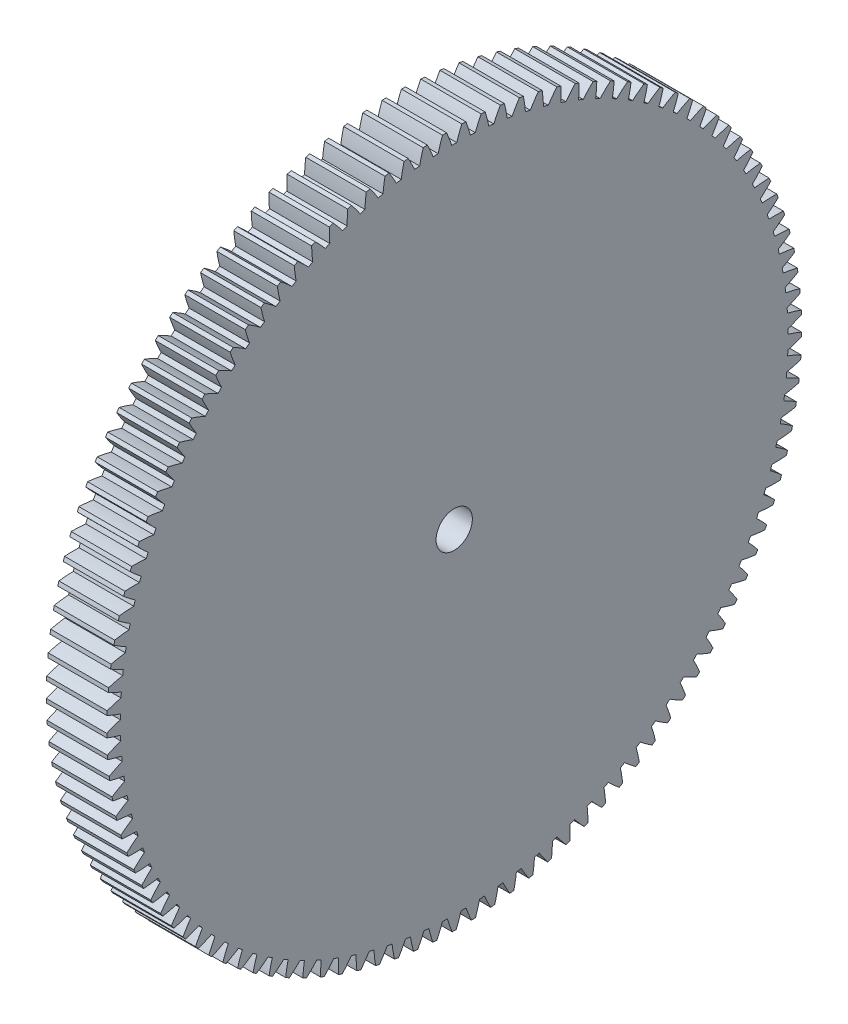
SolidWorks part; units mm, degrees
material "1.0035 (S185)"
ref_plane "Plane1" through (0, 0, 0) normal (0, 0, 1) x (1, 0, 0)
ref_plane "Plane2" through (0, 0, 0) normal (0, 1, 0) x (1, 0, 0)
ref_plane "Plane3" through (0, 0, 0) normal (1, 0, 0) x (0, 0, -1)
sketch "HoldingSke" plane through (0, 0, 0) normal (0, 1, 0) x (1, 0, 0)
  line L0 (0, 0) -> (-0.7815, -1.841)
  line L1 (-15, 0) -> (100, 0) construction
  line L2 (0, 0) -> (-2.1039, 2.3779)
  line L3 (0, 0) -> (-11.863, 4.5341)
  line L4 (0, 0) -> (-3.3744, 7.9495)
  line L5 (0, 0) -> (-46.8476, -17.4728)
  line L6 (0, 0) -> (-4.1448, -2.7965)
  line L7 (-2.1039, 2.3779) -> (8.6586, 51.2059)
  line L8 (-76.2, 54.61) -> (-75.7, 54.61)
  line L9 (-71.009, 38.7566) -> (-53.1078, 45.2721)
  line L10 (-76.2, 71.12) -> (104.1128, 71.12)
  line L11 (0, 0) -> (-5, 0)
  line L12 (-76.2, 101.6) -> (-76.181, 101.6)
  line L13 (24.9733, 27.94) -> (52.9518, 28.4284)
  line L14 (24.9733, 27.94) -> (24.9743, 27.94)
  line L15 (24.9733, 27.94) -> (100.4006, 29.5858)
  line L16 (-63.627, -0.5) -> (-12.827, -0.5)
  circle A0 centre (0, 0) radius 1.5
  circle A1 centre (0, 0) radius 27.624
  circle A2 centre (0, 0) radius 37.5
  circle A3 centre (0, 0) radius 1.5
  dimension "MHD" = 55.248
  dimension "Hub_dia" = 75
  dimension "Bore" = 3
  dimension "MBD" = 3
  dimension "Num_teeth" = 113
  dimension "Pitch_radius" = 180.3128
  dimension "Pitch" = 2
  dimension "Width" = 5
  dimension "Overall_len" = 50
  dimension "Show_teeth" = 113
  dimension "Thickness" = 5
  dimension "OAL" = 50.0001
  dimension "T_dim" = 0.5
  dimension "Ap" = 20
  dimension "H" = 19.05
  dimension "Backlash" = 0.019
  dimension "Addendum_fac" = 1
  dimension "Dedendum_fac" = 1.25
  dimension "Clearance_fac" = 0.25
  dimension "Dedendum_add" = 0.001
  dimension "Module" = 0.5
sketch "BasProSke" plane through (0, 0, 0) normal (0, 1, 0) x (1, 0, 0)
  line L0 (-10, 0) -> (60, 0) construction
  line L1 (0, 0) -> (0, 28.75)
  line L2 (0, 0) -> (5, 0)
  line L3 (5, 0) -> (5, 28.75)
  line L4 (5, 28.75) -> (0, 28.75)
  dimension "Diameter" = 57.5
  dimension "Thickness" = 5
revolve "Base-Revolve" add sketch "BasProSke" angle 360 about L0
sketch "TooCutSke" plane through (0, 0, 0) normal (1, 0, 0) x (0, 0, -1)
  line L1 (0, 0) -> (0, 107) construction
  line L2 (0, 0) -> (-0.4259, 28.2468) construction
  line L3 (0, 0) -> (-1.5705, 56.4736) construction
  line L4 (-0.4259, 28.2468) -> (-0.7852, 28.2368) construction
  arc A0 (0.2058, 27.6232) -> (-0.2058, 27.6232) centre (0, 0) ccw
  arc A1 (0.6425, 28.7682) -> (-0.6425, 28.7682) centre (0, 0) ccw
  circle A2 centre (0, 0) radius 28.25 construction
  circle A3 centre (0, 0) radius 26.5463 construction
  arc A4 (-0.2058, 27.6232) -> (-0.6425, 28.7682) centre (-10.9669, 24.1751) ccw
  arc A5 (0.6425, 28.7682) -> (0.2058, 27.6232) centre (10.9669, 24.1751) ccw
  dimension "Root_dia" = 55.248
  dimension "Overcut_dia" = 57.5508
  dimension "Pitch_dia" = 56.5
  dimension "Base_dia" = 53.0926
  dimension "Flank_rad" = 11.3
  dimension "Half_ang" = 1.593
  dimension "Half_CT" = 0.3594
extrude "ToothCut" cut sketch "TooCutSke" along normal through all
fillet "Breaks" [suppressed] radius 0.01
fillet "RootFillets" [suppressed] radius 0.126
pattern_circular "TeethCuts" count 113 every 3.186 about axis through (-10, 0, 0) along (1, 0, 0) of "ToothCut", "RootFillets", "Breaks"
sketch "HubNeaOneSke" plane through (0, 0, 0) normal (-1, 0, 0) x (0, 0, 1)
  circle A0 centre (0, 0) radius 27.624
  dimension "Diameter" = 55.248
extrude "HubNearOne" [suppressed] add sketch "HubNeaOneSke" along normal blind 45.0001
sketch "HubNeaBotSke" plane through (0, 0, 0) normal (-1, 0, 0) x (0, 0, 1)
  circle A0 centre (0, 0) radius 27.624
  dimension "Diameter" = 55.248
extrude "HubNearBoth" [suppressed] add sketch "HubNeaBotSke" along normal blind 22.5
ref_plane "FarPln" through (5, 0, 0) normal (1, 0, 0) x (0, 0, -1)
sketch "HubFarSke" plane through (5, 0, 0) normal (1, 0, 0) x (0, 0, -1)
  circle A0 centre (0, 0) radius 27.624
  dimension "Diameter" = 55.248
extrude "HubFar" [suppressed] add sketch "HubFarSke" along normal blind 22.5
sketch "BorSke" plane through (0, 0, 0) normal (1, 0, 0) x (0, 0, -1)
  circle A0 centre (0, 0) radius 1.5
  dimension "Diameter" = 3
extrude "Bore" cut sketch "BorSke" along normal mid plane 100.0001
sketch "KeySke" plane through (0, 0, 0) normal (1, 0, 0) x (0, 0, -1)
  line L0 (-0.6, 0) -> (-0.6, 2)
  line L1 (-0.6, 2) -> (0.6, 2)
  line L2 (0.6, 2) -> (0.6, 0)
  line L3 (0, 0) -> (0, 34) construction
  line L4 (-0.6, 0) -> (0.6, 0)
  dimension "Offset" = 2
  dimension "Width" = 1.2
extrude "Keyway" [suppressed] cut sketch "KeySke" along normal mid plane 100.0001
pattern_circular "Keyway2" [suppressed] count 2 every 90 about axis through (-10, 0, 0) along (1, 0, 0)
equation "' \"Module@HoldingSke\" = 6.35"
equation "' \"Num_teeth@HoldingSke\" = 12"
equation "' \"Ap@HoldingSke\" =  20"
equation "' \"Width@HoldingSke\" = 0.5 * 25.4"
equation "' \"Hub_dia@HoldingSke\"= 1 * 25.4"
equation "' \"Overall_len@HoldingSke\" = 1.0 * 25.4"
equation "' \"Bore@HoldingSke\" = 0.75 * 25.4"
equation "' \"T_dim@HoldingSke\" = 0.1 * 25.4"
equation "' \"Width@KeySke\" = 0.25 * 25.4"
equation "' \"Show_teeth@HoldingSke\" = 13"
equation "' \"Backlash@HoldingSke\" = 0.009 * 25.4"
equation "' \"Addendum_fac@HoldingSke\" = 1.0"
equation "' \"Dedendum_fac@HoldingSke\" = 1.25"
equation "' \"Dedendum_add@HoldingSke\" = 0.00005 * 25.4"
equation "' \"Clearance_fac@HoldingSke\" = 0.25"
equation "\"Pitch@HoldingSke\" = 1 / \"Module@HoldingSke\""
equation "\"Overcut_dia@TooCutSke\" = (\"Num_teeth@HoldingSke\" + 2 * \"Addendum_fac@HoldingSke\") / \"Pitch@HoldingSke\" + 0.002 * 25.4"
equation "\"Pitch_dia@TooCutSke\" = \"Num_teeth@HoldingSke\" / \"Pitch@HoldingSke\""
equation "\"Base_dia@TooCutSke\" = \"Num_teeth@HoldingSke\" / \"Pitch@HoldingSke\" * cos((\"Ap@HoldingSke\"  * 3.14159265 / 180))"
equation "\"Root_dia@TooCutSke\" = (\"Num_teeth@HoldingSke\" + 2) / \"Pitch@HoldingSke\" - 2 * (\"Addendum_fac@HoldingSke\" + \"Dedendum_fac@HoldingSke\") / \"Pitch@HoldingSke\" - \"Dedendum_add@HoldingSke\" * 2"
equation "\"Half_ang@TooCutSke\" = 180 / \"Num_teeth@HoldingSke\""
equation "\"Half_CT@TooCutSke\" = \"Num_teeth@HoldingSke\" / \"Pitch@HoldingSke\" * sin((3.14159265 / 2 / \"Num_teeth@HoldingSke\")) / 2 - 7 * \"Backlash@HoldingSke\" / 4"
equation "\"Flank_rad@TooCutSke\" = \"Num_teeth@HoldingSke\" / \"Pitch@HoldingSke\" / 5"
equation "\"Radius@RootFillets\" = \"Clearance_fac@HoldingSke\" / \"Pitch@HoldingSke\" + \"Dedendum_add@HoldingSke\""
equation "\"Break_rad@Breaks\" = 0.02 / \"Pitch@HoldingSke\""
equation "\"Thickness@HoldingSke\" = \"Width@HoldingSke\""
equation "\"OAL@HoldingSke\" = \"Thickness@HoldingSke\""
equation "\"MHD@HoldingSke\" = (\"Num_teeth@HoldingSke\" + 2) / \"Pitch@HoldingSke\" - 2 * (\"Addendum_fac@HoldingSke\" + \"Dedendum_fac@HoldingSke\")  / \"Pitch@HoldingSke\" - \"Dedendum_add@HoldingSke\" * 2"
equation "\"MBD@HoldingSke\" = (\"Num_teeth@HoldingSke\" + 2) / \"Pitch@HoldingSke\" - 2 * (\"Addendum_fac@HoldingSke\" + \"Dedendum_fac@HoldingSke\")  / \"Pitch@HoldingSke\" - \"Dedendum_add@HoldingSke\" * 2 - 0.002 * 25.4"
equation "\"MHD@HoldingSke\" = ((sgn( \"MHD@HoldingSke\" - \"Hub_dia@HoldingSke\" )-1)*( \"MHD@HoldingSke\" - \"Hub_dia@HoldingSke\" ))/-2+ \"Hub_dia@HoldingSke\""
equation "\"MBD@HoldingSke\" = ((sgn( \"MBD@HoldingSke\" - \"Bore@HoldingSke\" )-1)*( \"MBD@HoldingSke\" - \"Bore@HoldingSke\" ))/-2+ \"Bore@HoldingSke\""
equation "\"OAL@HoldingSke\" = ((sgn( \"OAL@HoldingSke\" - \"Overall_len@HoldingSke\" )+1)*( \"OAL@HoldingSke\" - \"Overall_len@HoldingSke\" ))/2 + \"Overall_len@HoldingSke\" + 0.000002 * 25.4"
equation "\"Num_teeth@TeethCuts\" = int( \"Show_teeth@HoldingSke\" ) + 1"
equation "\"Num_teeth@TeethCuts\" = ((sgn( \"Num_teeth@TeethCuts\" - \"Num_teeth@HoldingSke\" )-1)*( \"Num_teeth@TeethCuts\" - \"Num_teeth@HoldingSke\" ))/-2+ \"Num_teeth@HoldingSke\""
equation "\"Num_teeth@TeethCuts\" = ((sgn( \"Num_teeth@TeethCuts\" - 2.0)+1)*( \"Num_teeth@TeethCuts\" - 2.0))/2 +2.0"
equation "\"Angle@TeethCuts\" = 360.0 / \"Num_teeth@HoldingSke\""
equation "\"Diameter@BasProSke\" = (\"Num_teeth@HoldingSke\" + 2 * \"Addendum_fac@HoldingSke\") / \"Pitch@HoldingSke\""
equation "\"Thickness@BasProSke\"  = \"Thickness@HoldingSke\""
equation "' \"Fillet_rad@BasProSke\" =  \"Thickness@HoldingSke\" * 0.05"
equation "\"MHD@HoldingSke\" = ((sgn( \"MHD@HoldingSke\" - \"Root_dia@TooCutSke\" )-1)*( \"MHD@HoldingSke\" - \"Root_dia@TooCutSke\" ))/-2+ \"Root_dia@TooCutSke\""
equation "\"Diameter@HubNeaOneSke\" = \"MHD@HoldingSke\""
equation "\"Length@HubNearOne\" = \"OAL@HoldingSke\" - \"Thickness@BasProSke\""
equation "\"Diameter@HubNeaBotSke\" = \"MHD@HoldingSke\""
equation "\"Length@HubNearBoth\" = ( \"OAL@HoldingSke\" - \"Thickness@BasProSke\" ) / 2.0"
equation "\"Thickness@FarPln\" = \"Thickness@BasProSke\""
equation "\"Diameter@HubFarSke\" = \"MHD@HoldingSke\""
equation "\"Length@HubFar\" = ( \"OAL@HoldingSke\" - \"Thickness@BasProSke\" ) / 2.0"
equation "\"Diameter@BorSke\" = \"MBD@HoldingSke\""
equation "\"D1@Bore\" = \"OAL@HoldingSke\" * 2.0"
equation "\"D1@Keyway\" = \"OAL@HoldingSke\" * 2.0"
equation "\"Offset@KeySke\" = \"T_dim@HoldingSke\" + \"MBD@HoldingSke\" / 2.0"
